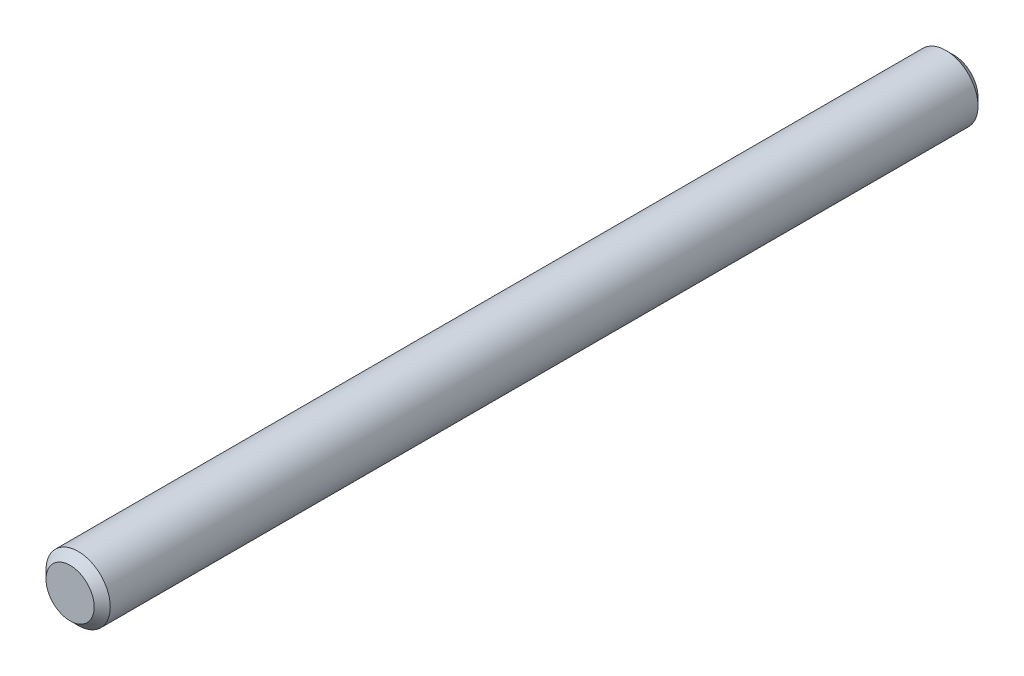
SolidWorks part; units mm, degrees
ref_plane "Plan de face" through (0, 0, 0) normal (0, 0, 1) x (1, 0, 0)
ref_plane "Plan de dessus" through (0, 0, 0) normal (0, 1, 0) x (1, 0, 0)
ref_plane "Plan de droite" through (0, 0, 0) normal (1, 0, 0) x (0, 0, -1)
sketch "Esquisse1" plane through (0, 0, 0) normal (0, 0, 1) x (1, 0, 0)
  circle A0 centre (0, 0) radius 0.4
  dimension "D1" = 0.8
extrude "Boss.-Extru.1" add sketch "Esquisse1" along normal blind 11
chamfer "Chanfrein1" distance 0.1 angle 45 2 edges at (0.4, 0, 0) (0.4, 0, 11)
